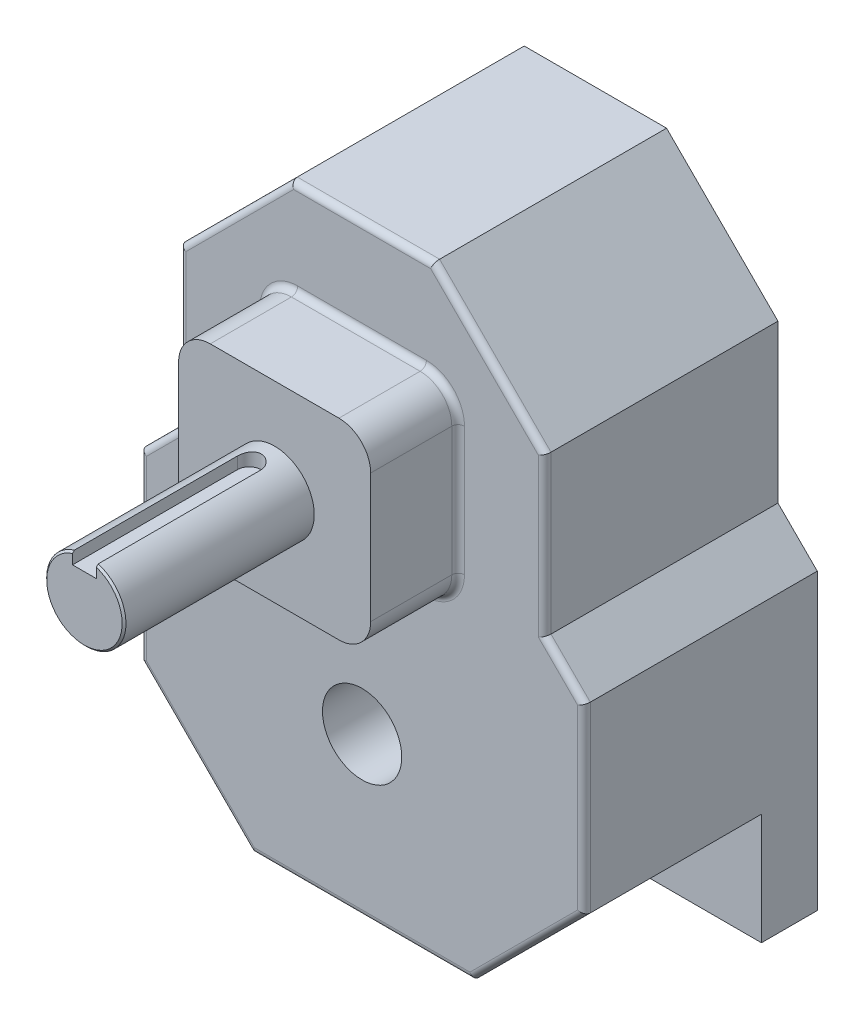
SolidWorks part; units mm, degrees
ref_plane "Front Plane" through (0, 0, 0) normal (0, 0, 1) x (1, 0, 0)
ref_plane "Top Plane" through (0, 0, 0) normal (0, 1, 0) x (1, 0, 0)
ref_plane "Right Plane" through (0, 0, 0) normal (1, 0, 0) x (0, 0, -1)
ref_plane "G" through (0, 63.5, 0) normal (0, 1, 0) x (-1, 0, 0)
ref_plane "E" through (0, 114.3, 0) normal (0, 1, 0) x (-1, 0, 0)
ref_plane "J" through (0, 152.4, 0) normal (0, 1, 0) x (-1, 0, 0)
ref_plane "B" through (0, 0, 46.736) normal (0, 0, 1) x (1, 0, 0)
ref_plane "C" through (0, 0, 102.362) normal (0, 0, 1) x (1, 0, 0)
ref_plane "A" through (0, 0, 64.262) normal (0, 0, 1) x (1, 0, 0)
sketch "L,M" plane through (0, 0, 0) normal (0, 0, 1) x (1, 0, 0)
  line L0 (45.8206, 152.4) -> (-14.2575, 152.4) construction
  line L1 (0, 0) -> (0, 63.5) construction
  line L2 (48.895, 63.5) -> (-48.895, 63.5) construction
  line L3 (-44.45, 31.75) -> (44.45, 31.75)
  line L4 (-14.2575, 152.4) -> (14.2575, 152.4)
  line L5 (48.895, 152.4) -> (-48.895, 152.4) construction
  line L6 (14.2575, 152.4) -> (36.576, 130.0815)
  line L7 (36.576, 130.0815) -> (36.576, 98.5185)
  line L8 (36.576, 98.5185) -> (44.45, 90.6445)
  line L9 (44.45, 90.6445) -> (44.45, 31.75)
  line L11 (45.8206, 152.4) -> (14.2575, 152.4) construction
  line L12 (-44.45, 90.6445) -> (-44.45, 31.75)
  line L13 (-36.576, 98.5185) -> (-44.45, 90.6445)
  line L14 (-36.576, 130.0815) -> (-36.576, 98.5185)
  line L15 (-14.2575, 152.4) -> (-36.576, 130.0815)
  line L16 (48.895, 114.3) -> (-48.895, 114.3) construction
  point P0 (-36.576, 114.3)
  point P7 (0, 31.75)
  point P23 (0, 152.4)
  dimension "D1" = 73.152
  dimension "D2" = 88.9
  dimension "D3" = 45
extrude "Boss-Extrude1" add sketch "L,M" along normal up to surface (46.736 mm away) up to plane "B"
sketch "Sketch3" plane through (0, 0, 46.736) normal (0, 0, 1) x (1, 0, 0)
  line L1 (48.895, 114.3) -> (-48.895, 114.3) construction
  line L2 (-19.2405, 133.5405) -> (19.2405, 133.5405)
  line L3 (-19.2405, 133.5405) -> (-19.2405, 95.0595)
  line L4 (-19.2405, 95.0595) -> (19.2405, 95.0595)
  line L5 (19.2405, 133.5405) -> (19.2405, 95.0595)
  line L6 (0, 114.3) -> (0, 0) construction
  line L7 (-19.2405, 133.5405) -> (19.2405, 95.0595) construction
  point P4 (0, 114.3)
  dimension "D1" = 38.481
extrude "Boss-Extrude2" add sketch "Sketch3" along normal up to surface (17.526 mm away) up to plane "A"
sketch "D" plane through (0, 0, 64.262) normal (0, 0, 1) x (1, 0, 0)
  line L0 (-19.2405, 133.5405) -> (19.2405, 95.0595) construction
  circle A0 centre (0, 114.3) radius 7.9375
  dimension "D1" = 15.875
extrude "Boss-Extrude3" add sketch "D" along normal up to surface (38.1 mm away) up to plane "C"
sketch "Sketch5" plane through (0, 0, 46.736) normal (0, 0, 1) x (1, 0, 0)
  line L0 (44.45, 54.0685) -> (22.1315, 31.75)
  line L1 (44.45, 31.75) -> (44.45, 90.6445) construction
  line L2 (-44.45, 31.75) -> (44.45, 31.75) construction
  line L3 (22.1315, 31.75) -> (44.45, 31.75)
  line L4 (44.45, 31.75) -> (44.45, 54.0685)
  line L5 (-14.2575, 152.4) -> (-36.576, 130.0815) construction
  line L6 (0, 31.75) -> (0, 114.3) construction
  line L7 (-44.45, 31.75) -> (-44.45, 54.0685)
  line L8 (-22.1315, 31.75) -> (-44.45, 31.75)
  line L9 (-44.45, 54.0685) -> (-22.1315, 31.75)
extrude "Cut-Extrude1" cut sketch "Sketch5" against normal blind 35.56
fillet "Fillet1" radius 6.35 4 edges at (-19.2405, 95.0595, 55.499) (19.2405, 95.0595, 55.499) (-19.2405, 133.5405, 55.499) (19.2405, 133.5405, 55.499)
fillet "Fillet2" radius 1.27 20 edges at (17.3806, 96.9194, 46.736) (19.2405, 114.3, 46.736) (17.3806, 131.6806, 46.736) (0, 133.5405, 46.736) (-17.3806, 131.6806, 46.736) (-19.2405, 114.3, 46.736) (-17.3806, 96.9194, 46.736) (0, 95.0595, 46.736) (-44.45, 72.3565, 46.736) (-40.513, 94.5815, 46.736) (-36.576, 114.3, 46.736) (-25.4168, 141.2408, 46.736) (0, 152.4, 46.736) (25.4168, 141.2408, 46.736) (36.576, 114.3, 46.736) (40.513, 94.5815, 46.736) (44.45, 72.3565, 46.736) (33.2908, 42.9092, 46.736) (0, 31.75, 46.736) (-33.2908, 42.9092, 46.736)
sketch "Sketch6" plane through (0, 114.3, 0) normal (0, 1, 0) x (-1, 0, 0)
  line L0 (0, 102.362) -> (0, 69.342) construction
  line L1 (48.895, 102.362) -> (-48.895, 102.362) construction
  line L2 (2.3876, 102.362) -> (2.3876, 69.342)
  line L3 (-2.3876, 102.362) -> (-2.3876, 69.342)
  line L4 (0, 0) -> (0, 69.342) construction
  line L6 (-14.2575, 0) -> (14.2575, 0) construction
  line L7 (48.895, 64.262) -> (-48.895, 64.262) construction
  arc A0 (2.3876, 102.362) -> (-2.3876, 102.362) centre (0, 102.362) ccw
  arc A1 (-2.3876, 69.342) -> (2.3876, 69.342) centre (0, 69.342) ccw
  point P4 (0, 85.852)
  dimension "D2" = 5.08
  dimension "D1" = 4.7752
extrude "Keyway" cut sketch "Sketch6" along normal through all from offset 5.1943
chamfer "Chamfer1" distance 0.381 angle 45 1 edges at (0, 106.3625, 102.362)
sketch "Sketch7" plane through (0, 0, 0) normal (0, 0, -1) x (-1, 0, 0)
  line L0 (48.895, 63.5) -> (-48.895, 63.5) construction
  line L1 (0, 63.5) -> (0, 114.3) construction
  circle A0 centre (0, 63.5) radius 7.9375
  circle A1 centre (0, 114.3) radius 7.9375 construction
extrude "Cut-Extrude3" cut sketch "Sketch7" against normal through all
